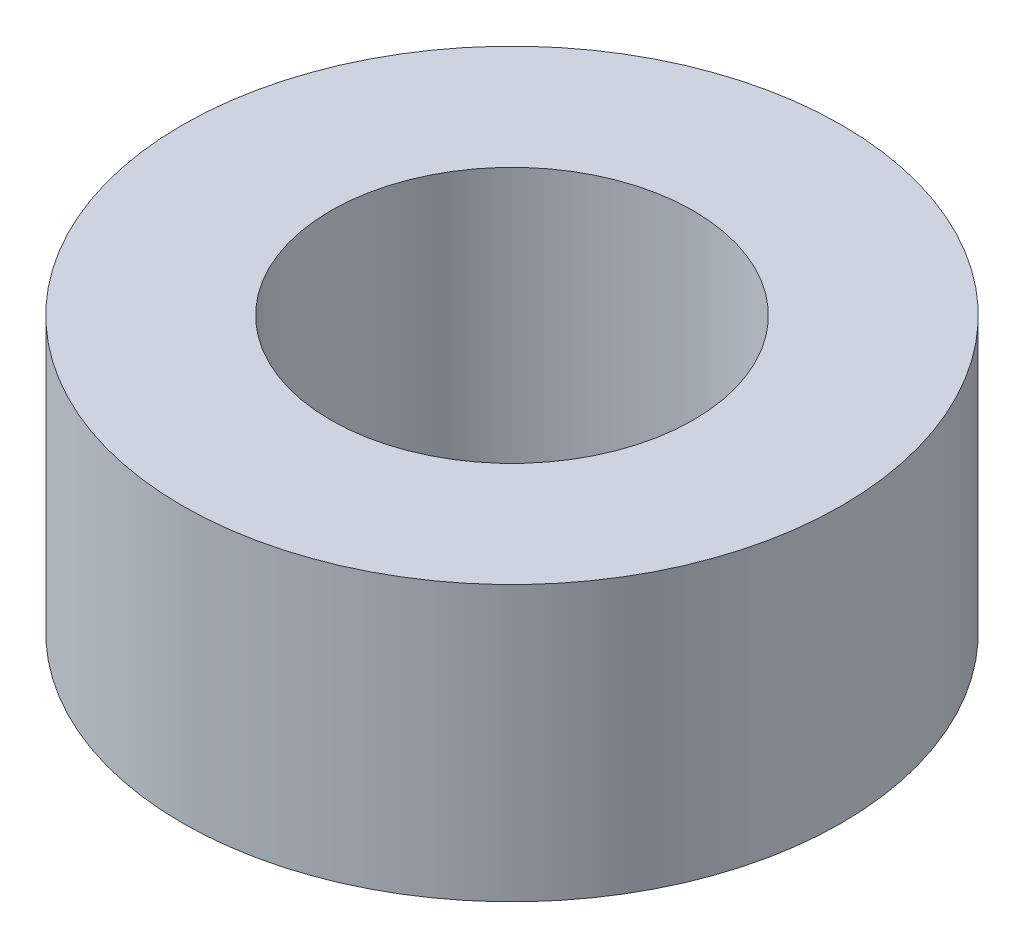
SolidWorks part; units mm, degrees
ref_plane "Front Plane" through (0, 0, 0) normal (0, 0, 1) x (1, 0, 0)
ref_plane "Top Plane" through (0, 0, 0) normal (0, 1, 0) x (1, 0, 0)
ref_plane "Right Plane" through (0, 0, 0) normal (1, 0, 0) x (0, 0, -1)
sketch "Sketch1" plane through (0, 0, 0) normal (0, 1, 0) x (1, 0, 0)
  circle A0 centre (0, 0) radius 3.3
  circle A1 centre (0, 0) radius 6
extrude "Boss-Extrude1" add sketch "Sketch1" along normal blind 5 contours A1 | A0
